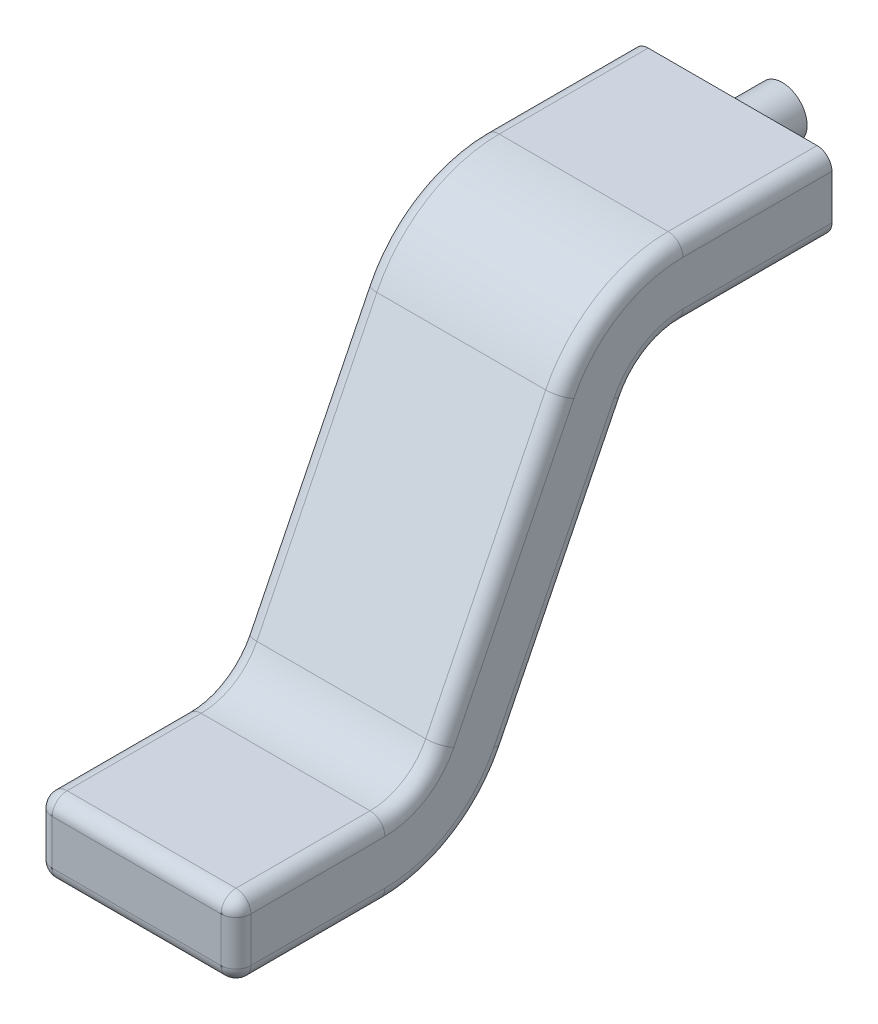
SolidWorks part; units mm, degrees
material "Aço inoxidável fundido"
ref_plane "Plano frontal" through (0, 0, 0) normal (0, 0, 1) x (1, 0, 0)
ref_plane "Plano superior" through (0, 0, 0) normal (0, 1, 0) x (1, 0, 0)
ref_plane "Plano direito" through (0, 0, 0) normal (1, 0, 0) x (0, 0, -1)
sketch "Esboço1" plane through (0, 0, 0) normal (0, 0, 1) x (1, 0, 0)
  line L1 (-0.17, -0.075) -> (0.17, -0.075)
  line L2 (-0.2, -0.045) -> (-0.2, 0.045)
  line L3 (-0.17, 0.075) -> (0.17, 0.075)
  line L4 (0.2, -0.045) -> (0.2, 0.045)
  line L5 (-0.2, -0.075) -> (0.2, 0.075) construction
  line L6 (-0.2, 0.075) -> (0.2, -0.075) construction
  arc A0 (-0.17, 0.075) -> (-0.2, 0.045) centre (-0.17, 0.045) ccw
  arc A1 (-0.2, -0.045) -> (-0.17, -0.075) centre (-0.17, -0.045) ccw
  arc A2 (0.17, -0.075) -> (0.2, -0.045) centre (0.17, -0.045) ccw
  arc A3 (0.17, 0.075) -> (0.2, 0.045) centre (0.17, 0.045) cw
  point P0 (0, 0)
  dimension "D3" = 0.03
  dimension "D1" = 0.4
  dimension "D2" = 0.15
sketch "Esboço2" plane through (0, 0, 0) normal (1, 0, 0) x (0, 0, -1)
  line L0 (0, 0) -> (0.3, 0)
  line L1 (0.4792, 0.1112) -> (0.7208, 0.5988)
  line L2 (0.9, 0.71) -> (1.2, 0.71)
  arc A0 (0.3, 0) -> (0.4792, 0.1112) centre (0.3, 0.2) ccw
  arc A1 (0.9, 0.71) -> (0.7208, 0.5988) centre (0.9, 0.51) ccw
  point P7 (0.4241, 0)
  point P10 (0.7759, 0.71)
  dimension "D5" = 0.2
  dimension "D1" = 0.3
  dimension "D2" = 0.6
  dimension "D3" = 0.3
  dimension "D4" = 0.71
sweep "Varredura1" add profiles "Esboço1" path "Esboço2"
fillet "Filete2" radius 0.03 8 edges at (0, 0.075, 0) (0.1912, 0.0662, 0) (0.2, 0, 0) (0.1912, -0.0662, 0) (0, -0.075, 0) (-0.1912, -0.0662, 0) (-0.2, 0, 0) (-0.1912, 0.0662, 0)
sketch "Esboço3" plane through (0, 0, -1.2) normal (0, 0, -1) x (-1, 0, 0)
  line L0 (0, 0.785) -> (0, 0.635) construction
  line L5 (0.2, 0.755) -> (0.2, 0.665) construction
  line L6 (-0.2, 0.665) -> (-0.2, 0.755) construction
  line L7 (-0.2, 0.71) -> (0.2, 0.71) construction
  line L8 (-0.17, 0.785) -> (0.17, 0.785) construction
  line L9 (0.17, 0.635) -> (-0.17, 0.635) construction
  circle A0 centre (0, 0.71) radius 0.05
  dimension "D1" = 0.1
extrude "Ressalto-extrusão1" add sketch "Esboço3" along normal blind 0.1
